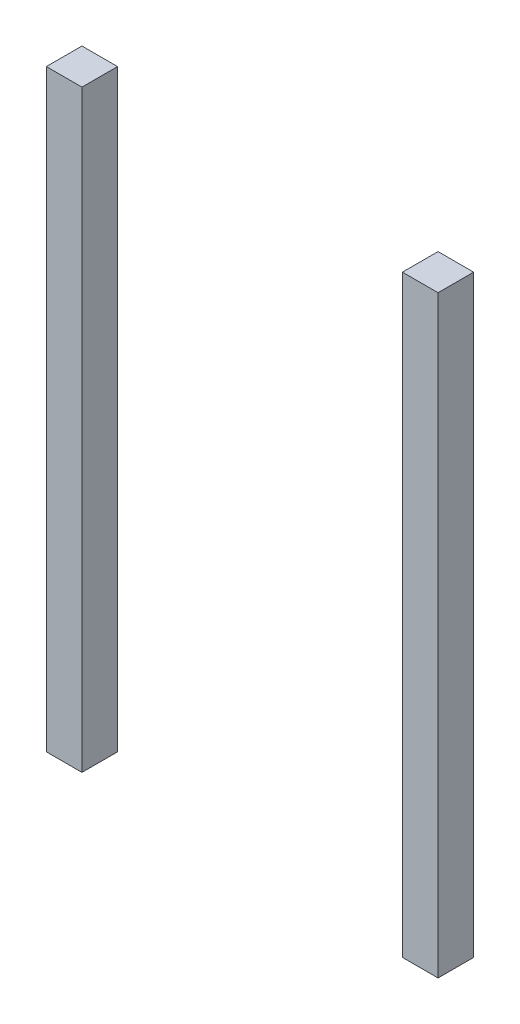
SolidWorks part; units mm, degrees
ref_plane "Ebene vorne" through (0, 0, 0) normal (0, 0, 1) x (1, 0, 0)
ref_plane "Ebene oben" through (0, 0, 0) normal (0, 1, 0) x (1, 0, 0)
ref_plane "Ebene rechts" through (0, 0, 0) normal (1, 0, 0) x (0, 0, -1)
sketch "Skizze1" plane through (0, 0, 0) normal (0, 0, 1) x (1, 0, 0)
  line L0 (0, 43.7615) -> (0, -102.1101) construction
  line L1 (-135, 250) -> (-165, 250)
  line L2 (-135, 250) -> (-135, -250)
  line L3 (-135, -250) -> (-165, -250)
  line L4 (-165, 250) -> (-165, -250)
  line L5 (-150, 250) -> (-150, -327.457) construction
  line L6 (165, 250) -> (165, -250)
  line L7 (135, -250) -> (165, -250)
  line L8 (135, 250) -> (135, -250)
  line L9 (135, 250) -> (165, 250)
  point P9 (-135, 0)
  dimension "D1" = 30
  dimension "D2" = 500
  dimension "D3" = 150
extrude "Aufsatz-Linear austragen1" add sketch "Skizze1" along normal blind 30
